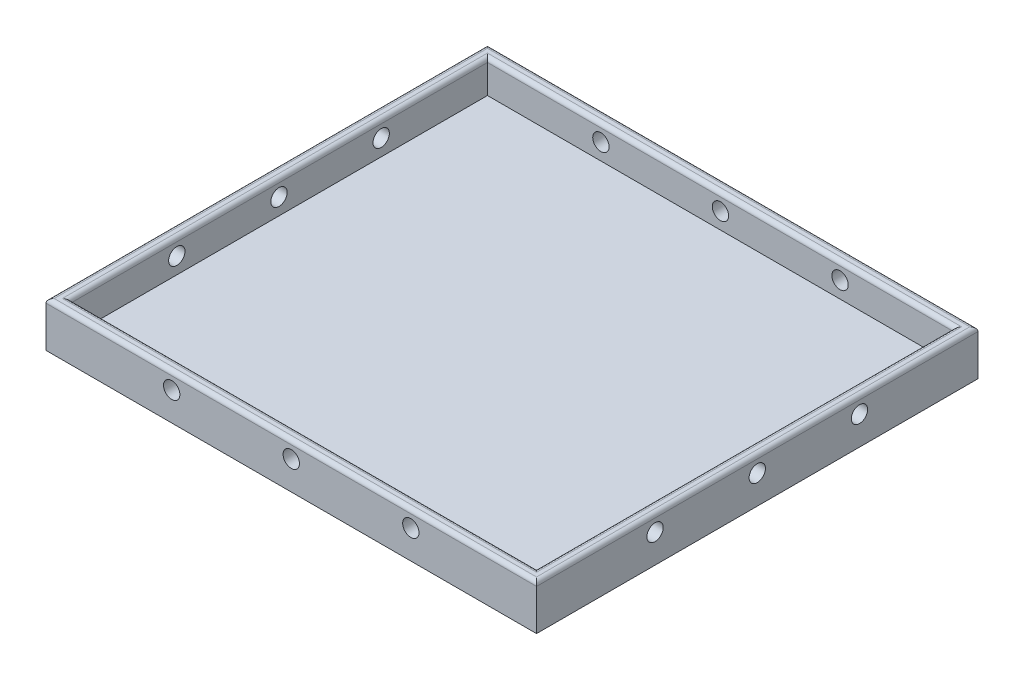
SolidWorks part; units mm, degrees
ref_plane "Front Plane" through (0, 0, 0) normal (0, 0, 1) x (1, 0, 0)
ref_plane "Top Plane" through (0, 0, 0) normal (0, 1, 0) x (1, 0, 0)
ref_plane "Right Plane" through (0, 0, 0) normal (1, 0, 0) x (0, 0, -1)
sketch "Sketch1" plane through (0, 0, 0) normal (0, 1, 0) x (1, 0, 0)
  line L1 (-201.6099, 77.8947) -> (-81.6099, 77.8947)
  line L2 (-201.6099, 77.8947) -> (-201.6099, -30.1053)
  line L3 (-201.6099, -30.1053) -> (-81.6099, -30.1053)
  line L4 (-81.6099, 77.8947) -> (-81.6099, -30.1053)
  dimension "D1" = 120
  dimension "D2" = 108
extrude "Boss-Extrude1" add sketch "Sketch1" along normal blind 11
sketch "Sketch4" plane through (0, 11, 0) normal (0, 1, 0) x (1, 0, 0)
  line L0 (-201.6099, 77.8947) -> (-201.6099, -30.1053) construction
  line L1 (-198.6099, 74.8947) -> (-84.6099, 74.8947)
  line L2 (-198.6099, 74.8947) -> (-198.6099, -27.1053)
  line L3 (-198.6099, -27.1053) -> (-84.6099, -27.1053)
  line L4 (-84.6099, 74.8947) -> (-84.6099, -27.1053)
  line L5 (-81.6099, 77.8947) -> (-201.6099, 77.8947) construction
  line L6 (-81.6099, -30.1053) -> (-81.6099, 77.8947) construction
  line L7 (-201.6099, -30.1053) -> (-81.6099, -30.1053) construction
  dimension "D1" = 3
  dimension "D2" = 3
  dimension "D3" = 3
  dimension "D4" = 3
extrude "Cut-Extrude1" cut sketch "Sketch4" against normal blind 8
sketch "Sketch5" plane through (0, 0, -74.8947) normal (0, 0, 1) x (1, 0, 0)
  line L0 (-198.6099, 3) -> (-198.6099, 11) construction
  line L1 (-84.6099, 3) -> (-198.6099, 3) construction
  circle A0 centre (-170.8599, 7) radius 2
  circle A1 centre (-141.6099, 7) radius 2
  circle A2 centre (-112.3599, 7) radius 2
  dimension "D1" = 27.75
  dimension "D2" = 29.25
  dimension "D3" = 29.25
  dimension "D4" = 4
  dimension "D5" = 4
  dimension "D6" = 4
sketch "Sketch6" plane through (-198.6099, 0, 0) normal (1, 0, 0) x (0, 0, -1)
  line L0 (-27.1053, 3) -> (-27.1053, 11) construction
  line L1 (74.8947, 3) -> (74.8947, 11) construction
  line L2 (74.8947, 3) -> (-27.1053, 3) construction
  circle A0 centre (-1.1053, 7) radius 2
  circle A1 centre (23.8947, 7) radius 2
  circle A2 centre (48.8947, 7) radius 2
  dimension "D1" = 26
  dimension "D2" = 25
  dimension "D3" = 25
  dimension "D4" = 26
  dimension "D5" = 4
extrude "Cut-Extrude6" cut sketch "Sketch6" against normal through all both and the other way through all
extrude "Cut-Extrude5" cut sketch "Sketch5" against normal through all both and the other way through all
fillet "Fillet2" radius 1 8 edges at (-141.6099, 11, 27.1053) (-141.6099, 11, 30.1053) (-81.6099, 11, -23.8947) (-84.6099, 11, -23.8947) (-198.6099, 11, -23.8947) (-141.6099, 11, -74.8947) (-201.6099, 11, -23.8947) (-141.6099, 11, -77.8947)
